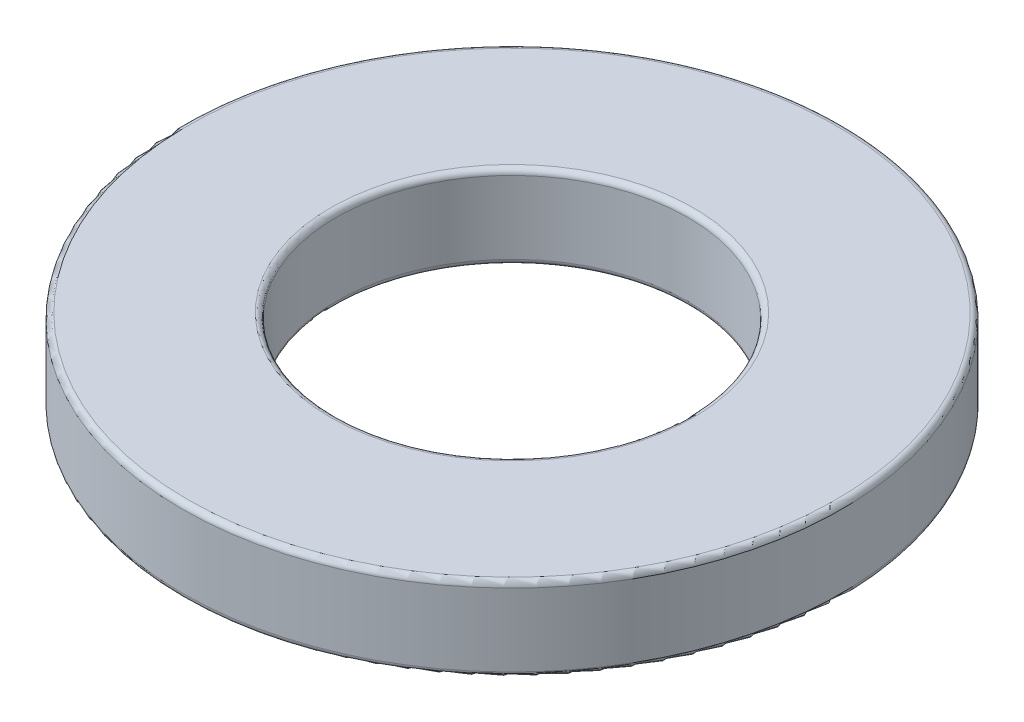
SolidWorks part; units mm, degrees
material "1023 Листовая углеродистая сталь (SS)"
ref_plane "Спереди" through (0, 0, 0) normal (0, 0, 1) x (1, 0, 0)
ref_plane "Сверху" through (0, 0, 0) normal (0, 1, 0) x (1, 0, 0)
ref_plane "Справа" through (0, 0, 0) normal (1, 0, 0) x (0, 0, -1)
sketch "Эскиз1" plane through (0, 0, 0) normal (0, 1, 0) x (1, 0, 0)
  circle A0 centre (0, 0) radius 3.15
  circle A1 centre (0, 0) radius 5.9
  dimension "D1" = 6.3
  dimension "D2" = 11.8
extrude "Бобышка-Вытянуть1" add sketch "Эскиз1" along normal blind 1.5
fillet "Скругление1" radius 0.1 4 edges at (0, 1.5, 3.15) (0, 0, 3.15) (0, 0, 5.9) (0, 1.5, 5.9)
